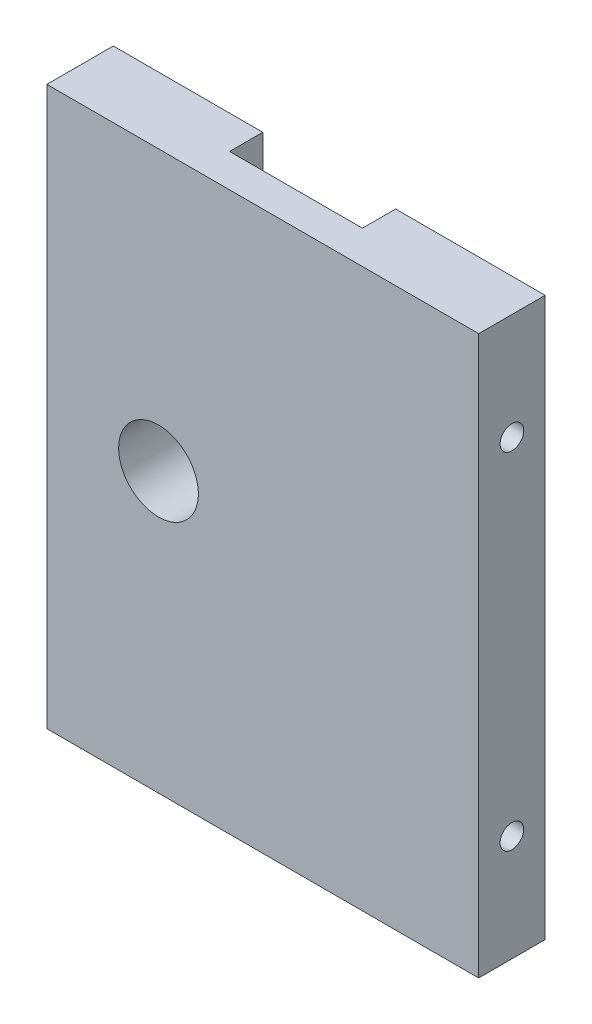
SolidWorks part; units mm, degrees
ref_plane "Front Plane" through (0, 0, 0) normal (0, 0, 1) x (1, 0, 0)
ref_plane "Top Plane" through (0, 0, 0) normal (0, 1, 0) x (1, 0, 0)
ref_plane "Right Plane" through (0, 0, 0) normal (1, 0, 0) x (0, 0, -1)
sketch "Sketch1" plane through (0, 0, 0) normal (0, 0, 1) x (1, 0, 0)
  line L1 (0, 0) -> (32.5, 0)
  line L2 (0, 0) -> (0, 42)
  line L3 (0, 42) -> (32.5, 42)
  line L4 (32.5, 0) -> (32.5, 42)
extrude "Boss-Extrude2" add sketch "Sketch1" along normal blind 5
sketch "Sketch2" plane through (0, 0, 5) normal (0, 0, 1) x (1, 0, 0)
  line L0 (0, 42) -> (0, 34)
  line L1 (0, 42) -> (0, 0) construction
  line L2 (0, 34) -> (32.5, 34)
  line L3 (32.5, 0) -> (32.5, 42) construction
  line L4 (0, 0) -> (0, 8)
  line L5 (0, 8) -> (32.5, 8)
sketch "Sketch3" plane through (0, 0, 0) normal (-1, 0, 0) x (0, 0, 1)
  line L0 (5, 34) -> (0, 34)
  line L1 (5, 42) -> (5, 34) construction
  line L2 (0, 42) -> (0, 0) construction
  line L3 (5, 8) -> (0, 8)
  line L4 (5, 0) -> (5, 8) construction
  line L5 (5, 42) -> (5, 0) construction
hole_wizard "#2-56 Tapped Hole1" positions "Sketch4" profile "Sketch5" tap size "#2-56" standard "ANSI Inch"
sketch "Sketch4" plane through (0, 0, 0) normal (-1, 0, 0) x (0, 0, 1)
  line L0 (5, 34) -> (0, 34) construction
  line L1 (5, 8) -> (0, 8) construction
  point P0 (2.5, 34)
  point P4 (2.5, 8)
sketch "Sketch5" plane through (0, 34, 2.5) normal (0, 1, 0) x (0, 0, 1)
  line L0 (0, 0) -> (0, 8)
  line L1 (0, 8) -> (0.889, 7.4658)
  line L2 (0.889, 7.4658) -> (0.889, 0)
  line L5 (0.889, 0) -> (0, 0)
  line L10 (0, 8) -> (-0.889, 7.4658) construction
  line L11 (0, -6.35) -> (0, 107.95) construction
  dimension "Tap Drill Dia." = 1.778
  dimension "Tap Drill Depth" = 8
  dimension "Drill Angle" = 118
cosmetic thread "Hole Thread1" parameters "D1"=4.37, "D2"=2.1844
cosmetic thread "Hole Thread2" parameters "D1"=4.37, "D2"=2.1844
sketch "Sketch6" plane through (32.5, 0, 0) normal (1, 0, 0) x (0, 0, -1)
  line L0 (-5, 34) -> (0, 34)
  line L1 (-5, 8) -> (0, 8)
hole_wizard "#2-56 Tapped Hole2" positions "Sketch7" profile "Sketch8" tap size "#2-56" standard "ANSI Inch"
sketch "Sketch7" plane through (32.5, 0, 0) normal (1, 0, 0) x (0, 0, -1)
  point P0 (-2.5, 34)
  point P3 (-2.5, 8)
sketch "Sketch8" plane through (32.5, 34, 2.5) normal (0, 1, 0) x (0, 0, -1)
  line L0 (0, 0) -> (0, 8)
  line L1 (0, 8) -> (0.889, 7.4658)
  line L2 (0.889, 7.4658) -> (0.889, 0)
  line L5 (0.889, 0) -> (0, 0)
  line L10 (0, 8) -> (-0.889, 7.4658) construction
  line L11 (0, -6.35) -> (0, 107.95) construction
  dimension "Tap Drill Dia." = 1.778
  dimension "Tap Drill Depth" = 8
  dimension "Drill Angle" = 118
cosmetic thread "Hole Thread3" parameters "D1"=4.37, "D2"=2.1844
cosmetic thread "Hole Thread4" parameters "D1"=4.37, "D2"=2.1844
sketch "Sketch9" plane through (0, 0, 0) normal (0, 0, -1) x (-1, 0, 0)
  line L0 (0, 21) -> (-32.5, 21)
  line L1 (0, 42) -> (0, 0) construction
  line L2 (-32.5, 0) -> (-32.5, 42) construction
  line L3 (-16.25, 21) -> (-8.4, 21)
  circle A0 centre (-8.4, 21) radius 3
extrude "Cut-Extrude1" cut sketch "Sketch9" against normal blind 5 contours L0 A0 | L0 A0
sketch "Sketch10" plane through (0, 0, 0) normal (0, 0, -1) x (-1, 0, 0)
  line L0 (-32.5, 42) -> (-21.25, 42)
  line L1 (-32.5, 42) -> (0, 42) construction
  line L2 (0, 42) -> (-11.25, 42)
  line L3 (-11.25, 42) -> (-11.25, 35.5)
  line L4 (-11.25, 35.5) -> (-21.25, 35.5)
  line L5 (-21.25, 35.5) -> (-21.25, 42)
  line L7 (-21.25, 42) -> (-11.25, 42)
  line L8 (-21.25, 42) -> (-21.25, 35.5)
  line L9 (-21.25, 35.5) -> (-11.25, 35.5)
  line L10 (-11.25, 42) -> (-11.25, 35.5)
  line M4 (0, 42) -> (-32.5, 42)
extrude "Cut-Extrude2" cut sketch "Sketch10" against normal blind 2.5 contours L5 L4 L3 M4
